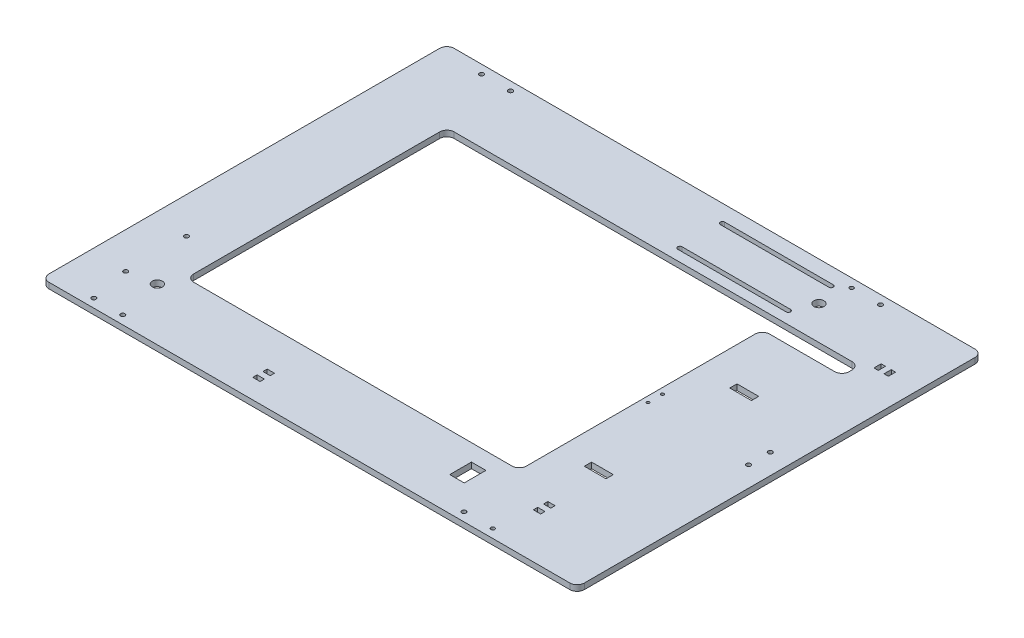
SolidWorks part; units mm, degrees
material "Pine"
ref_plane "Front Plane" through (0, 0, 0) normal (0, 0, 1) x (1, 0, 0)
ref_plane "Top Plane" through (0, 0, 0) normal (0, 1, 0) x (1, 0, 0)
ref_plane "Right Plane" through (0, 0, 0) normal (1, 0, 0) x (0, 0, -1)
sketch "Sketch1" plane through (0, 0, 0) normal (0, 1, 0) x (1, 0, 0)
  line L1 (0, 0) -> (370, 0)
  line L2 (0, 0) -> (0, 280)
  line L3 (0, 280) -> (370, 280)
  line L4 (370, 0) -> (370, 280)
  line L5 (50, 50) -> (280, 50)
  line L6 (50, 50) -> (50, 230)
  line L7 (50, 230) -> (280, 230)
  line L8 (280, 50) -> (280, 230)
  line L9 (50, 280) -> (50, 274) construction
  line L10 (50, 274) -> (30, 274) construction
  line L12 (185, 280) -> (185, 0) construction
  line L13 (0, 140) -> (370, 140) construction
  line L14 (284, 140) -> (284, 145) construction
  line L15 (284, 140) -> (284, 135) construction
  circle A0 centre (30, 274) radius 1.5
  circle A1 centre (50, 274) radius 1.5692
  circle A2 centre (30, 6) radius 1.5
  circle A3 centre (50, 6) radius 1.5
  circle A4 centre (285.7569, 273.9854) radius 1.3573
  circle A5 centre (305.7569, 273.9346) radius 1.5
  circle A6 centre (285.7569, 6.0015) radius 1.5
  circle A7 centre (305.7569, 6.0068) radius 1.3225
  circle A8 centre (284, 145) radius 1
  circle A9 centre (284, 135) radius 1
  dimension "D11" = 3
  dimension "D12" = 2
  dimension "D1" = 370
  dimension "D2" = 280
  dimension "D3" = 230
  dimension "D4" = 50
  dimension "D5" = 50
  dimension "D6" = 50
  dimension "D8" = 6
  dimension "D10" = 20
  dimension "D13" = 4
  dimension "D14" = 10
  dimension "D15" = 20
  dimension "D16" = 20
  dimension "D17" = 20
extrude "Boss-Extrude1" add sketch "Sketch1" along normal blind 4
sketch "Sketch2" plane through (0, 4, 0) normal (0, 1, 0) x (1, 0, 0)
  line L1 (280, 230) -> (335, 230)
  line L2 (280, 230) -> (280, 218)
  line L3 (280, 218) -> (335, 218)
  line L4 (335, 230) -> (335, 218)
  dimension "D1" = 55
  dimension "D2" = 12
extrude "Cut-Extrude1" cut sketch "Sketch2" against normal blind 10
sketch "Sketch3" plane through (0, 4, 0) normal (0, 1, 0) x (1, 0, 0)
  line L0 (356, 140) -> (356, 147.5) construction
  line L1 (370, 0) -> (370, 280) construction
  line L3 (356, 147.5) -> (356, 140) construction
  line L6 (356, 140) -> (356, 132.5) construction
  circle A0 centre (356, 147.5) radius 1.5
  circle A1 centre (356, 132.5) radius 1.5
  dimension "D1" = 3
  dimension "D2" = 3
  dimension "D3" = 14
  dimension "D4" = 15
extrude "Cut-Extrude2" cut sketch "Sketch3" against normal blind 10
sketch "Sketch4" plane through (0, 4, 0) normal (0, 1, 0) x (1, 0, 0)
  line L0 (277.5, 280) -> (277.5, 268) construction
  line L1 (370, 280) -> (0, 280) construction
  line L2 (277.5, 280) -> (277.5, 238.5) construction
  line L3 (277.5, 268) -> (202.5, 268) construction
  line L4 (277.5, 266.5) -> (202.5, 266.5)
  line L5 (277.5, 269.5) -> (202.5, 269.5)
  line L6 (277.5, 238.5) -> (202.5, 238.5) construction
  line L7 (277.5, 237) -> (202.5, 237)
  line L8 (277.5, 240) -> (202.5, 240)
  line L9 (370, 0) -> (370, 280) construction
  arc A0 (277.5, 266.5) -> (277.5, 269.5) centre (277.5, 268) ccw
  arc A1 (202.5, 269.5) -> (202.5, 266.5) centre (202.5, 268) ccw
  arc A2 (277.5, 237) -> (277.5, 240) centre (277.5, 238.5) ccw
  arc A3 (202.5, 240) -> (202.5, 237) centre (202.5, 238.5) ccw
  point P6 (240, 268)
  point P11 (240, 238.5)
  dimension "D1" = 12
  dimension "D2" = 41.5
  dimension "D3" = 3
  dimension "D4" = 3
  dimension "D5" = 75
  dimension "D6" = 130
extrude "Cut-Extrude3" cut sketch "Sketch4" against normal blind 10
fillet "Fillet3" radius 5 1 edges at (370, 2, 0)
fillet "Fillet4" radius 5 1 edges at (370, 2, -280)
fillet "Fillet5" radius 5 1 edges at (0, 2, 0)
fillet "Fillet6" radius 5 1 edges at (0, 2, -280)
fillet "Fillet7" radius 5 1 edges at (280, 2, -218)
fillet "Fillet8" radius 5 1 edges at (280, 2, -50)
fillet "Fillet9" radius 5 4 edges at (335, 2, -218) (335, 2, -230) (50, 2, -230) (50, 2, -50)
sketch "Sketch6" plane through (0, 0, 0) normal (0, -1, 0) x (1, 0, 0)
  line L0 (279, -268) -> (279, -238.5) construction
  circle A0 centre (283.8523, -253.25) radius 3.5
  arc A1 (277.5, -269.5) -> (277.5, -266.5) centre (277.5, -268) ccw construction
  arc A2 (277.5, -240) -> (277.5, -237) centre (277.5, -238.5) ccw construction
  dimension "D1" = 7
extrude "Cut-Extrude4" cut sketch "Sketch6" against normal blind 10
sketch "Sketch7" plane through (0, 0, 0) normal (0, -1, 0) x (1, 0, 0)
  circle A0 centre (43.5283, -36.3572) radius 3.5
  dimension "D1" = 7
extrude "Cut-Extrude5" cut sketch "Sketch7" against normal blind 10
sketch "Sketch8" plane through (0, 0, 0) normal (0, -1, 0) x (1, 0, 0)
  line L1 (132.3588, -13.485) -> (137.3588, -13.485)
  line L2 (132.3588, -13.485) -> (132.3588, -16.485)
  line L3 (132.3588, -16.485) -> (137.3588, -16.485)
  line L4 (137.3588, -13.485) -> (137.3588, -16.485)
  line L5 (132.3588, -20.485) -> (137.3588, -20.485)
  line L6 (132.3588, -20.485) -> (132.3588, -23.485)
  line L7 (132.3588, -23.485) -> (137.3588, -23.485)
  line L8 (137.3588, -20.485) -> (137.3588, -23.485)
  line L9 (258.6011, -23.3631) -> (268.6011, -23.3631)
  line L10 (258.6011, -23.3631) -> (258.6011, -38.3631)
  line L11 (258.6011, -38.3631) -> (268.6011, -38.3631)
  line L12 (268.6011, -23.3631) -> (268.6011, -38.3631)
  line L20 (308.6025, -31.1591) -> (313.6025, -31.1591)
  line L21 (308.6025, -31.1591) -> (308.6025, -34.1591)
  line L22 (308.6025, -34.1591) -> (313.6025, -34.1591)
  line L23 (313.6025, -31.1591) -> (313.6025, -34.1591)
  line L24 (308.6025, -38.1591) -> (313.6025, -38.1591)
  line L25 (308.6025, -38.1591) -> (308.6025, -41.1591)
  line L26 (308.6025, -41.1591) -> (313.6025, -41.1591)
  line L27 (313.6025, -38.1591) -> (313.6025, -41.1591)
  line L28 (315.1261, -74.8595) -> (300.1261, -74.8595)
  line L29 (341.3593, -233.7592) -> (344.3593, -233.7592)
  line L30 (341.3593, -233.7592) -> (341.3593, -238.7592)
  line L31 (341.3593, -238.7592) -> (344.3593, -238.7592)
  line L32 (344.3593, -233.7592) -> (344.3593, -238.7592)
  line L33 (348.3593, -238.7592) -> (351.3593, -238.7592)
  line L34 (348.3593, -238.7592) -> (348.3593, -233.7592)
  line L35 (348.3593, -233.7592) -> (351.3593, -233.7592)
  line L36 (351.3593, -238.7592) -> (351.3593, -233.7592)
  line L37 (318.5539, -171.9384) -> (303.5539, -171.9384)
  line L38 (318.5539, -171.9384) -> (318.5539, -176.9384)
  line L39 (318.5539, -176.9384) -> (303.5539, -176.9384)
  line L40 (303.5539, -171.9384) -> (303.5539, -176.9384)
  line L41 (315.1261, -74.8595) -> (315.1261, -79.8595)
  line L42 (315.1261, -79.8595) -> (300.1261, -79.8595)
  line L43 (300.1261, -74.8595) -> (300.1261, -79.8595)
  point P8 (134.8588, -16.485)
  point P30 (311.1025, -34.1591)
  dimension "D1" = 5
  dimension "D2" = 3
  dimension "D3" = 4
  dimension "D4" = 15
  dimension "D5" = 10
  dimension "D6" = 4
  dimension "D7" = 5
  dimension "D8" = 3
  dimension "D9" = 5
  dimension "D10" = 3
  dimension "D11" = 4
  dimension "D12" = 5
  dimension "D13" = 15
  dimension "D14" = 5
  dimension "D15" = 15
extrude "Cut-Extrude6" cut sketch "Sketch8" against normal blind 10
sketch "Sketch9" plane through (0, 0, 0) normal (0, -1, 0) x (1, 0, 0)
  line L0 (25, -75) -> (50, -75) construction
  line L3 (25, -33) -> (25, -75) construction
  line L4 (50, -225) -> (50, -55) construction
  line L5 (50, -75) -> (50, -55) construction
  circle A0 centre (25, -33) radius 1.5
  circle A1 centre (25, -75) radius 1.5
  dimension "D4" = 3
  dimension "D1" = 20
  dimension "D2" = 25
  dimension "D3" = 42
extrude "Cut-Extrude7" cut sketch "Sketch9" against normal blind 10
sketch "Sketch12" plane through (0, 4, 0) normal (0, 1, 0) x (1, 0, 0)
  line L0 (731.5136, 140.1347) -> (204.6283, -31.0608) construction
  line L1 (150, 220) -> (750, 220) construction
  line L2 (101.7785, 146.432) -> (955.1118, 146.432) construction
  line L3 (101.0183, 781.5728) -> (101.0183, 227.5728) construction
  line L4 (213.3333, 206.5) -> (1066.6667, 206.5) construction
  line L5 (1035.1327, 94.0566) -> (181.7993, 94.0566) construction
